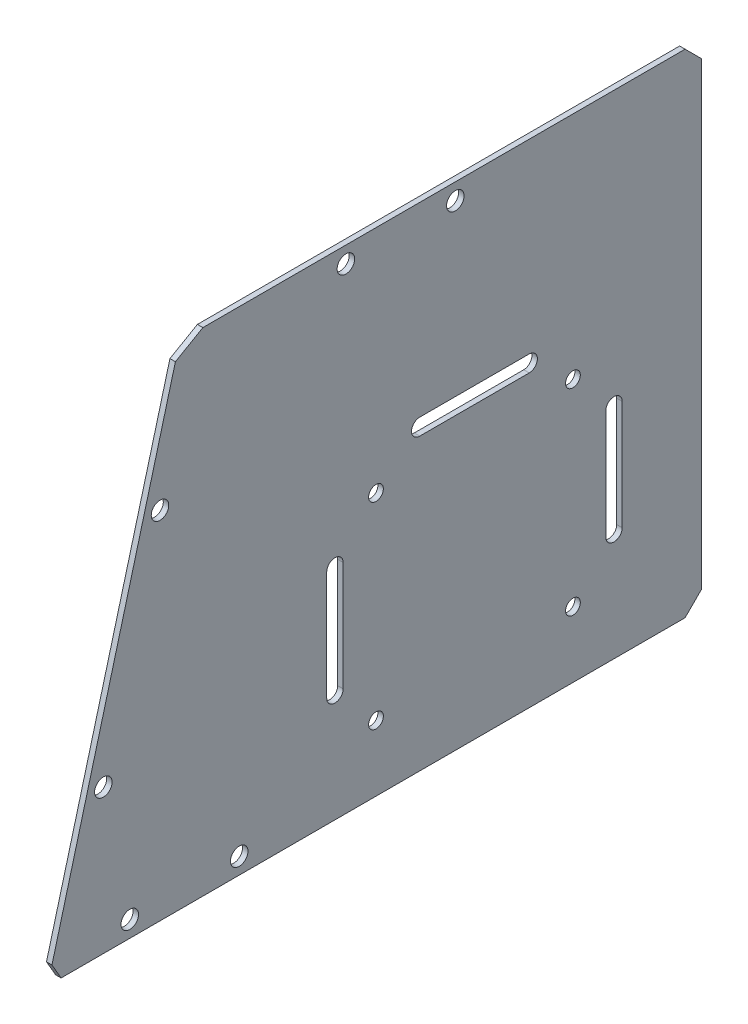
SolidWorks part; units mm, degrees
material "Hexcel AS4C (3000 丝)"
ref_plane "前视基准面" through (0, 0, 0) normal (0, 0, 1) x (1, 0, 0)
ref_plane "上视基准面" through (0, 0, 0) normal (0, 1, 0) x (1, 0, 0)
ref_plane "右视基准面" through (0, 0, 0) normal (1, 0, 0) x (0, 0, -1)
sketch "草图1" plane through (0, 0, 0) normal (1, 0, 0) x (0, 0, -1)
  line L0 (0, 0) -> (17, 0) construction
  line L1 (0, 0) -> (0, -30.5) construction
  line L2 (17, -30.5) -> (31.5, -30.5) construction
  line L4 (-12, 7.5) -> (48, 7.5)
  line L5 (-12, 7.5) -> (-12, -36.5)
  line L6 (-12, -36.5) -> (48, -36.5)
  line L7 (48, 7.5) -> (48, -36.5)
  line L8 (18, -36.5) -> (18, 7.5) construction
  line L9 (-12, -14.5) -> (48, -14.5) construction
  circle A0 centre (0, 0) radius 1.6
  circle A1 centre (17, 0) radius 1.6
  circle A2 centre (0, -30.5) radius 1.6
  circle A3 centre (17, -30.5) radius 1.6
  circle A4 centre (31.5, -30.5) radius 1.6
  point P257 (18, -14.5)
  dimension "D1" = 3.2
  dimension "D2" = 17
  dimension "D5" = 30.5
  dimension "D6" = 14.5
  dimension "D7" = 6
  dimension "D8" = 12
  dimension "D9" = 60
  dimension "D10" = 44
  dimension "D3" = 2
  dimension "D4" = 2
extrude "凸台-拉伸1" add sketch "草图1" along normal blind 1
sketch "草图2" plane through (1, 0, 0) normal (1, 0, 0) x (0, 0, -1)
  line L0 (-12, 7.5) -> (-12, -36.5) construction
  line L1 (48, 7.5) -> (-86.5, 7.5)
  line L2 (48, 7.5) -> (48, 97.5)
  line L3 (48, 97.5) -> (-86.5, 97.5)
  line L4 (-86.5, 7.5) -> (-86.5, 97.5)
  line L5 (-19.25, 97.5) -> (-19.25, 7.5) construction
  line L6 (48, 52.5) -> (-86.5, 52.5) construction
  point P288 (-19.25, 52.5)
  dimension "D1" = 90
  dimension "D2" = 74.5
extrude "凸台-拉伸2" add sketch "草图2" against normal up to surface (1 mm away) up to face at (0, -14.5, -18)
sketch "草图3" plane through (0, 0, 0) normal (-1, 0, 0) x (0, 0, 1)
  line L0 (86.5, 7.5) -> (62.3846, 97.5)
  line L1 (86.5, 97.5) -> (-48, 97.5) construction
  line L2 (62.3846, 97.5) -> (86.5, 97.5)
  line L3 (86.5, 97.5) -> (86.5, 7.5)
  dimension "D1" = 15
extrude "切除-拉伸1" cut sketch "草图3" against normal through all
sketch "草图4" plane through (0, 0, 0) normal (-1, 0, 0) x (0, 0, 1)
  line L0 (85.6962, 10.5) -> (-48, 10.5) construction
  line L1 (62.3846, 97.5) -> (86.5, 7.5) construction
  line L2 (-48, -36.5) -> (-48, 97.5) construction
  line L3 (12, 7.5) -> (86.5, 7.5) construction
  line L4 (71.5, 10.5) -> (51.5, 10.5) construction
  line L5 (63.1884, 94.5) -> (-48, 94.5) construction
  line L6 (62.3846, 97.5) -> (86.5, 7.5) construction
  line L7 (-48, -36.5) -> (-48, 97.5) construction
  line L8 (-48, 97.5) -> (62.3846, 97.5) construction
  line L9 (59.2787, 97.5) -> (83.3942, 7.5) construction
  line L10 (86.5, 7.5) -> (12, 7.5) construction
  line L11 (65.9775, 72.5) -> (76.3302, 33.863) construction
  circle A0 centre (71.5, 10.5) radius 1.6
  circle A1 centre (51.5, 10.5) radius 1.6
  circle A2 centre (12, 94.5) radius 1.6
  circle A3 centre (32, 94.5) radius 1.6
  circle A4 centre (65.9775, 72.5) radius 1.6
  circle A5 centre (76.3302, 33.863) radius 1.6
  dimension "D2" = 3.2
  dimension "D6" = 3.2
  dimension "D10" = 2
  dimension "D1" = 3
  dimension "D3" = 15
  dimension "D4" = 20
  dimension "D5" = 3
  dimension "D7" = 20
  dimension "D8" = 60
  dimension "D9" = 3
  dimension "D11" = 25
  dimension "D13" = 40
  dimension "D12" = 2
extrude "切除-拉伸2" cut sketch "草图4" against normal through all
sketch "草图5" plane through (1, 0, 0) normal (1, 0, 0) x (0, 0, -1)
  line L0 (-86.5, 7.5) -> (-12, 7.5) construction
  line L1 (-26.5, 55.5) -> (9.5, 55.5) construction
  line L2 (-26.5, 55.5) -> (-26.5, 19.5) construction
  line L3 (-26.5, 19.5) -> (9.5, 19.5) construction
  line L4 (9.5, 55.5) -> (9.5, 19.5) construction
  line L5 (-8.5, 19.5) -> (-8.5, 55.5) construction
  line L6 (-26.5, 37.5) -> (9.5, 37.5) construction
  circle A0 centre (-26.5, 55.5) radius 1.35
  circle A1 centre (9.5, 55.5) radius 1.35
  circle A2 centre (9.5, 19.5) radius 1.35
  circle A3 centre (-26.5, 19.5) radius 1.35
  point P0 (-8.5, 37.5)
  dimension "D2" = 2.7
  dimension "D1" = 36
  dimension "D3" = 30
  dimension "D4" = 60
extrude "切除-拉伸3" cut sketch "草图5" against normal through all
sketch "草图6" plane through (1, 0, 0) normal (1, 0, 0) x (0, 0, -1)
  line L0 (-86.5, 7.5) -> (-12, 7.5) construction
  line L1 (48, 97.5) -> (33, 97.5)
  line L2 (48, 97.5) -> (48, 7.5)
  line L3 (48, 7.5) -> (33, 7.5)
  line L4 (33, 97.5) -> (33, 7.5)
  line L5 (40.5, 7.5) -> (40.5, 97.5) construction
  line L6 (48, 52.5) -> (33, 52.5) construction
  point P304 (40.5, 52.5)
  dimension "D1" = 15
extrude "切除-拉伸4" cut sketch "草图6" against normal through all and the other way through all
chamfer "倒角1" [suppressed] distance 3 angle 45
sketch "草图7" plane through (1, 0, 0) normal (1, 0, 0) x (0, 0, -1)
  line L1 (0, 0) -> (17, 0) construction
  line L2 (0, 0) -> (0, -30.5) construction
  line L3 (0, -30.5) -> (17, -30.5) construction
  line L4 (17, 0) -> (17, -30.5) construction
  line L5 (8.5, -30.5) -> (8.5, 0) construction
  line L6 (0, -15.25) -> (17, -15.25) construction
  line L8 (4, -4) -> (13, -4)
  line L9 (4, -4) -> (4, -26.5)
  line L10 (4, -26.5) -> (13, -26.5)
  line L11 (13, -4) -> (13, -26.5)
  line L12 (8.5, -26.5) -> (8.5, -4) construction
  line L13 (4, -15.25) -> (13, -15.25) construction
  point P5 (8.5, -15.25)
  point P144 (8.5, -15.25)
  dimension "D1" = 4
  dimension "D2" = 4
extrude "切除-拉伸5" cut sketch "草图7" against normal through all
fillet "圆角1" radius 2 4 edges at (0.5, -26.5, -4) (0.5, -4, -13) (0.5, -26.5, -13) (0.5, -4, -4)
sketch "草图8" plane through (1, 0, 0) normal (1, 0, 0) x (0, 0, -1)
  line L0 (-12, 7.5) -> (33, 7.5)
  line L16 (33, 7.5) -> (33, 97.5)
  line L18 (33, 97.5) -> (-62.3846, 97.5)
  line L20 (-62.3846, 97.5) -> (-86.5, 7.5)
  line L22 (-86.5, 7.5) -> (-12, 7.5)
  line L23 (-12, 7.5) -> (-12, -36.5)
  line L25 (-12, -36.5) -> (48, -36.5)
  line L27 (48, -36.5) -> (48, 7.5)
  line L29 (48, 7.5) -> (33, 7.5)
  line L38 (-12, 7.5) -> (-12, -36.5)
  line L40 (-12, -36.5) -> (48, -36.5)
  line L42 (48, -36.5) -> (48, 7.5)
  line L44 (48, 7.5) -> (33, 7.5)
  dimension "D1" = 0
extrude "切除-拉伸6" cut sketch "草图8" against normal through all
sketch "草图9" plane through (1, 0, 0) normal (1, 0, 0) x (0, 0, -1)
  line L0 (-18.5, 62) -> (1.5, 62) construction
  line L1 (-26.5, 55.5) -> (9.5, 55.5) construction
  line L2 (-26.5, 55.5) -> (-26.5, 19.5) construction
  line L3 (-26.5, 19.5) -> (9.5, 19.5) construction
  line L4 (9.5, 55.5) -> (9.5, 19.5) construction
  line L5 (-8.5, 19.5) -> (-8.5, 55.5) construction
  line L6 (-26.5, 37.5) -> (9.5, 37.5) construction
  line L7 (-18.5, 63.5) -> (1.5, 63.5)
  line L8 (-29, 57) -> (12, 57) construction
  line L9 (-29, 57) -> (-29, 18) construction
  line L10 (-29, 18) -> (12, 18) construction
  line L11 (12, 57) -> (12, 18) construction
  line L12 (-8.5, 23) -> (-8.5, 62) construction
  line L13 (-29, 37.5) -> (12, 37.5) construction
  line L14 (-18.5, 60.5) -> (1.5, 60.5)
  line L15 (-34, 47.5) -> (-34, 27.5) construction
  line L16 (-32.5, 47.5) -> (-32.5, 27.5)
  line L17 (-35.5, 47.5) -> (-35.5, 27.5)
  line L18 (17, 47.5) -> (17, 27.5) construction
  line L19 (15.5, 47.5) -> (15.5, 27.5)
  line L20 (18.5, 47.5) -> (18.5, 27.5)
  arc A0 (-18.5, 63.5) -> (-18.5, 60.5) centre (-18.5, 62) ccw
  arc A1 (1.5, 60.5) -> (1.5, 63.5) centre (1.5, 62) ccw
  arc A2 (-32.5, 47.5) -> (-35.5, 47.5) centre (-34, 47.5) ccw
  arc A3 (-35.5, 27.5) -> (-32.5, 27.5) centre (-34, 27.5) ccw
  arc A4 (15.5, 47.5) -> (18.5, 47.5) centre (17, 47.5) cw
  arc A5 (18.5, 27.5) -> (15.5, 27.5) centre (17, 27.5) cw
  point P5 (-8.5, 37.5)
  point P9 (-8.5, 62)
  point P21 (-34, 37.5)
  point P28 (17, 37.5)
  point P188 (-8.5, 37.5)
  dimension "D4" = 5
  dimension "1.5" = 1.5
  dimension "D5" = 1.5
  dimension "D1" = 39
  dimension "41" = 41
  dimension "D2" = 19.5
  dimension "D3" = 20
  dimension "20.5" = 20.5
  dimension "20" = 20
  dimension "D6" = 5
extrude "切除-拉伸7" cut sketch "草图9" against normal through all
chamfer "倒角2" distance 3 angle 45 4 edges at (0.5, 7.5, -33) (0.5, 97.5, -33) (0.5, 97.5, 62.3846) (0.5, 7.5, 86.5)
